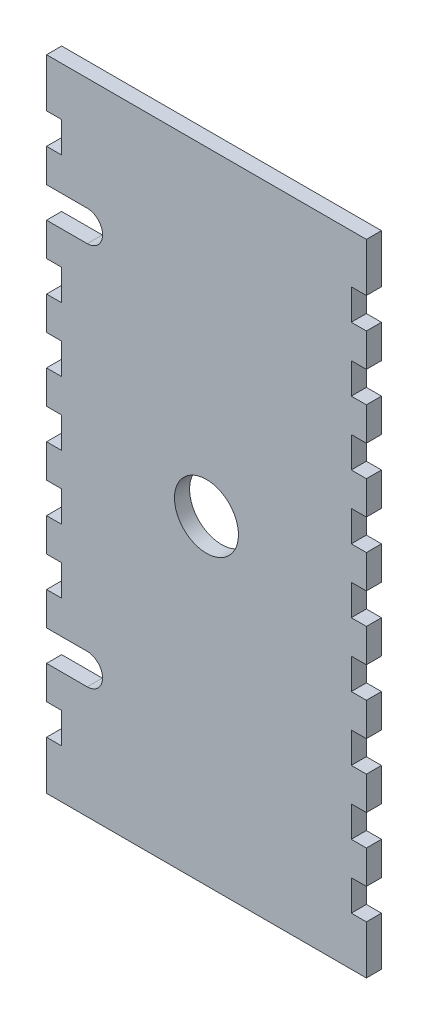
SolidWorks part; units mm, degrees
ref_plane "Front Plane" through (0, 0, 0) normal (0, 0, 1) x (1, 0, 0)
ref_plane "Top Plane" through (0, 0, 0) normal (0, 1, 0) x (1, 0, 0)
ref_plane "Right Plane" through (0, 0, 0) normal (1, 0, 0) x (0, 0, -1)
sketch "Sketch1" plane through (0, 0, 0) normal (0, 0, 1) x (1, 0, 0)
  line L0 (0, 0) -> (0, -9.652)
  line L1 (0, 0) -> (63.5, 0)
  line L2 (0, -22.352) -> (2.9972, -22.352)
  line L3 (0, -127) -> (63.5, -127)
  line L4 (2.9972, -22.352) -> (2.9972, -28.448) construction
  line L5 (0, -9.652) -> (2.9972, -9.652)
  line L6 (2.9972, -9.652) -> (2.9972, -15.748)
  line L7 (2.9972, -15.748) -> (0, -15.748)
  line L8 (0, -15.748) -> (0, -22.352)
  line L9 (2.9972, -28.448) -> (0, -28.448)
  line L10 (0, -28.448) -> (0, -35.052)
  line L11 (0, -35.052) -> (2.9972, -35.052)
  line L12 (2.9972, -35.052) -> (2.9972, -41.148)
  line L13 (2.9972, -41.148) -> (0, -41.148)
  line L14 (0, -41.148) -> (0, -47.752)
  line L15 (0, -47.752) -> (2.9972, -47.752)
  line L16 (2.9972, -47.752) -> (2.9972, -53.848)
  line L17 (2.9972, -53.848) -> (0, -53.848)
  line L18 (0, -53.848) -> (0, -60.452)
  line L19 (0, -60.452) -> (2.9972, -60.452)
  line L20 (2.9972, -60.452) -> (2.9972, -66.548)
  line L21 (2.9972, -66.548) -> (0, -66.548)
  line L22 (0, -66.548) -> (0, -73.152)
  line L23 (0, -73.152) -> (2.9972, -73.152)
  line L24 (2.9972, -73.152) -> (2.9972, -79.248)
  line L25 (2.9972, -79.248) -> (0, -79.248)
  line L26 (31.75, 0) -> (31.75, -127) construction
  line L27 (0, -79.248) -> (0, -85.852)
  line L28 (0, -85.852) -> (2.9972, -85.852)
  line L29 (2.9972, -85.852) -> (2.9972, -91.948)
  line L30 (2.9972, -91.948) -> (0, -91.948)
  line L31 (0, -91.948) -> (0, -98.552)
  line L32 (0, -98.552) -> (2.9972, -98.552)
  line L33 (2.9972, -98.552) -> (2.9972, -104.648) construction
  line L34 (2.9972, -104.648) -> (0, -104.648)
  line L35 (0, -104.648) -> (0, -111.252)
  line L36 (0, -111.252) -> (2.9972, -111.252)
  line L37 (2.9972, -111.252) -> (2.9972, -117.348)
  line L38 (2.9972, -117.348) -> (0, -117.348)
  line L39 (0, -117.348) -> (0, -127)
  line L40 (63.5, -117.348) -> (63.5, -127)
  line L41 (60.5028, -117.348) -> (63.5, -117.348)
  line L42 (60.5028, -111.252) -> (60.5028, -117.348)
  line L43 (63.5, -111.252) -> (60.5028, -111.252)
  line L44 (63.5, -104.648) -> (63.5, -111.252)
  line L45 (60.5028, -104.648) -> (63.5, -104.648)
  line L46 (60.5028, -98.552) -> (60.5028, -104.648)
  line L47 (63.5, -98.552) -> (60.5028, -98.552)
  line L48 (63.5, -91.948) -> (63.5, -98.552)
  line L49 (60.5028, -91.948) -> (63.5, -91.948)
  line L50 (60.5028, -85.852) -> (60.5028, -91.948)
  line L51 (63.5, -85.852) -> (60.5028, -85.852)
  line L52 (63.5, -79.248) -> (63.5, -85.852)
  line L53 (60.5028, -79.248) -> (63.5, -79.248)
  line L54 (60.5028, -73.152) -> (60.5028, -79.248)
  line L55 (63.5, -73.152) -> (60.5028, -73.152)
  line L56 (63.5, -66.548) -> (63.5, -73.152)
  line L57 (60.5028, -66.548) -> (63.5, -66.548)
  line L58 (60.5028, -60.452) -> (60.5028, -66.548)
  line L59 (63.5, -60.452) -> (60.5028, -60.452)
  line L60 (63.5, -53.848) -> (63.5, -60.452)
  line L61 (60.5028, -53.848) -> (63.5, -53.848)
  line L62 (60.5028, -47.752) -> (60.5028, -53.848)
  line L63 (63.5, -47.752) -> (60.5028, -47.752)
  line L64 (63.5, -41.148) -> (63.5, -47.752)
  line L65 (60.5028, -41.148) -> (63.5, -41.148)
  line L66 (60.5028, -35.052) -> (60.5028, -41.148)
  line L67 (63.5, -35.052) -> (60.5028, -35.052)
  line L68 (63.5, -28.448) -> (63.5, -35.052)
  line L69 (60.5028, -28.448) -> (63.5, -28.448)
  line L70 (63.5, -15.748) -> (63.5, -22.352)
  line L71 (60.5028, -15.748) -> (63.5, -15.748)
  line L72 (60.5028, -9.652) -> (60.5028, -15.748)
  line L73 (63.5, -9.652) -> (60.5028, -9.652)
  line L74 (60.5028, -22.352) -> (60.5028, -28.448)
  line L75 (63.5, -22.352) -> (60.5028, -22.352)
  line L76 (63.5, 0) -> (63.5, -9.652)
  line L77 (2.9972, -22.352) -> (8.0772, -22.352)
  line L78 (2.9972, -28.448) -> (8.0772, -28.448)
  line L79 (2.9972, -98.552) -> (8.0772, -98.552)
  line L80 (2.9972, -104.648) -> (8.0772, -104.648)
  line L164 (0, -117.348) -> (0, -123.952) [skipped]
  arc A0 (8.0772, -22.352) -> (8.0772, -28.448) centre (8.0772, -25.4) cw
  arc A1 (8.0772, -98.552) -> (8.0772, -104.648) centre (8.0772, -101.6) cw
  circle A2 centre (31.75, -63.5) radius 6.35
  dimension "D13" = 12.7
  dimension "D1" = 63.5
  dimension "D2" = 127
  dimension "D3" = 9.652
  dimension "D4" = 6.096
  dimension "D5" = 2.9972
  dimension "D6" = 6.604
  dimension "D8" = 5.08
  dimension "D9" = 5.08
  dimension "D10" = 2
  dimension "D7" = 9
extrude "Boss-Extrude2" add sketch "Sketch1" along normal blind 2.9972
